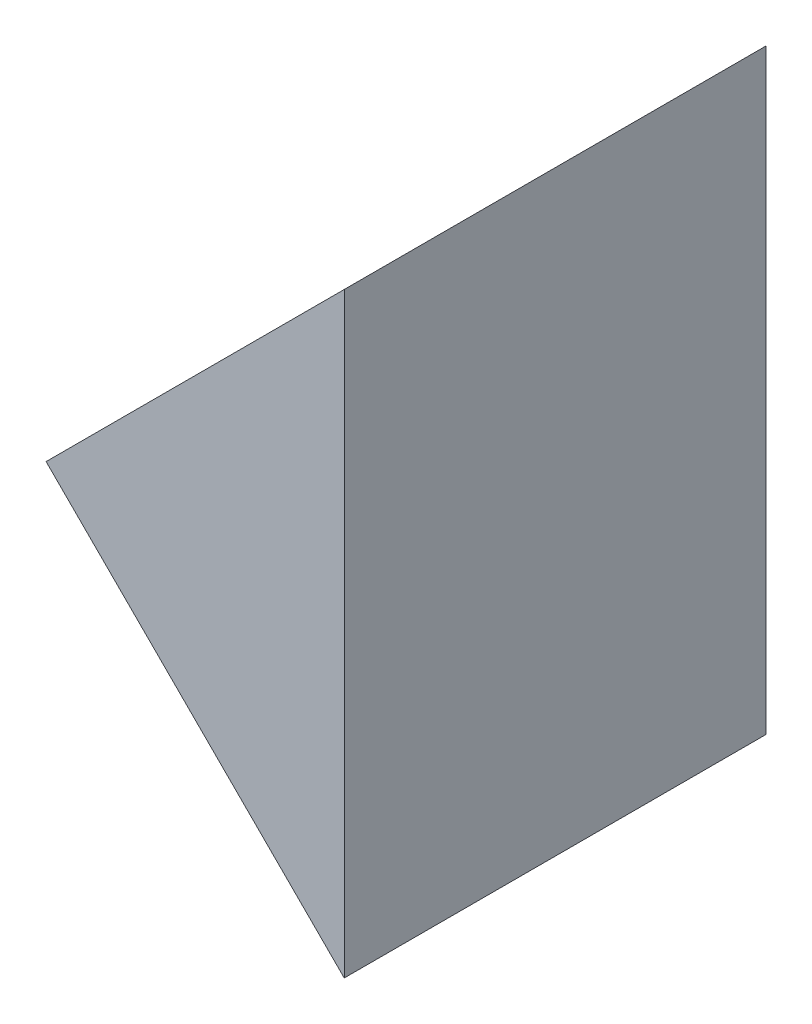
SolidWorks part; units mm, degrees
ref_plane "前视基准面" through (0, 0, 0) normal (0, 0, 1) x (1, 0, 0)
ref_plane "上视基准面" through (0, 0, 0) normal (0, 1, 0) x (1, 0, 0)
ref_plane "右视基准面" through (0, 0, 0) normal (1, 0, 0) x (0, 0, -1)
sketch "草图1" plane through (0, 0, 0) normal (0, 0, 1) x (1, 0, 0)
  line L0 (110.9533, 27.5514) -> (118.0244, 34.6225)
  line L1 (110.9533, 27.5514) -> (118.0244, 20.4803)
  line L2 (118.0244, 20.4803) -> (118.0244, 34.6225)
  dimension "D1" = 10
  dimension "D2" = 10
extrude "凸台-拉伸1" add sketch "草图1" along normal blind 10
